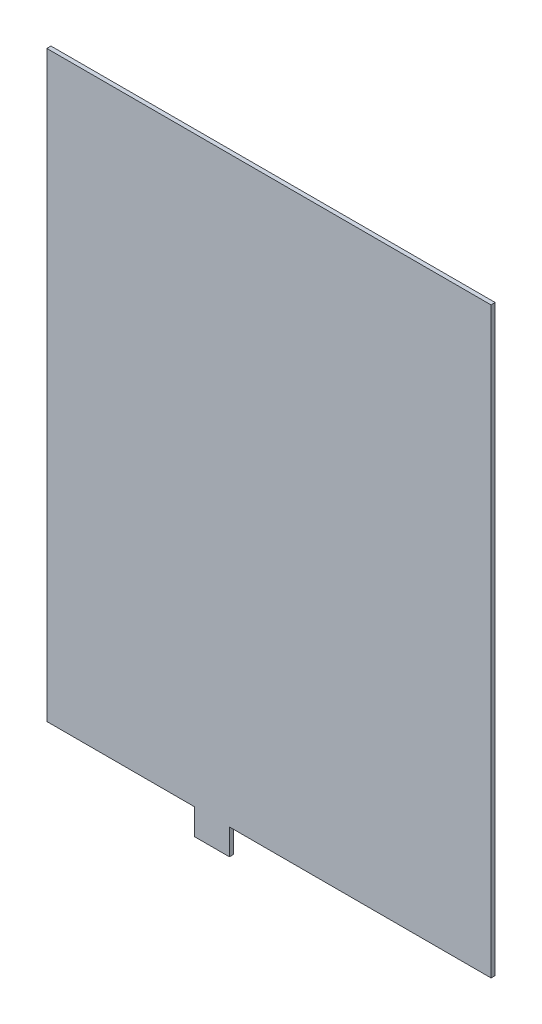
SolidWorks part; units mm, degrees
material "Стекло"
ref_plane "Front" through (0, 0, 0) normal (0, 0, 1) x (1, 0, 0)
ref_plane "Top" through (0, 0, 0) normal (0, 1, 0) x (1, 0, 0)
ref_plane "Right" through (0, 0, 0) normal (1, 0, 0) x (0, 0, -1)
sketch "Эскиз1" plane through (0, 0, 0) normal (0, 0, 1) x (1, 0, 0)
  line L1 (85.75, -112.5) -> (-85.75, -112.5)
  line L2 (85.75, -112.5) -> (85.75, 112.5)
  line L3 (85.75, 112.5) -> (-85.75, 112.5)
  line L4 (-85.75, -112.5) -> (-85.75, 112.5)
  line L5 (85.75, -112.5) -> (-85.75, 112.5) construction
  line L6 (85.75, 112.5) -> (-85.75, -112.5) construction
  line L7 (-28.75, -112.5) -> (-28.75, -122.5)
  line L8 (-28.75, -122.5) -> (-15.25, -122.5)
  line L9 (-15.25, -122.5) -> (-15.25, -112.5)
  point P0 (0, 0)
  dimension "D1" = 225
  dimension "D2" = 171.5
  dimension "D3" = 10
  dimension "D4" = 57
  dimension "D5" = 101
extrude "Бобышка-Вытянуть1" add sketch "Эскиз1" along normal blind 1.6 contours L4 L1 L2 L3 | L8 L9 L1 L7
